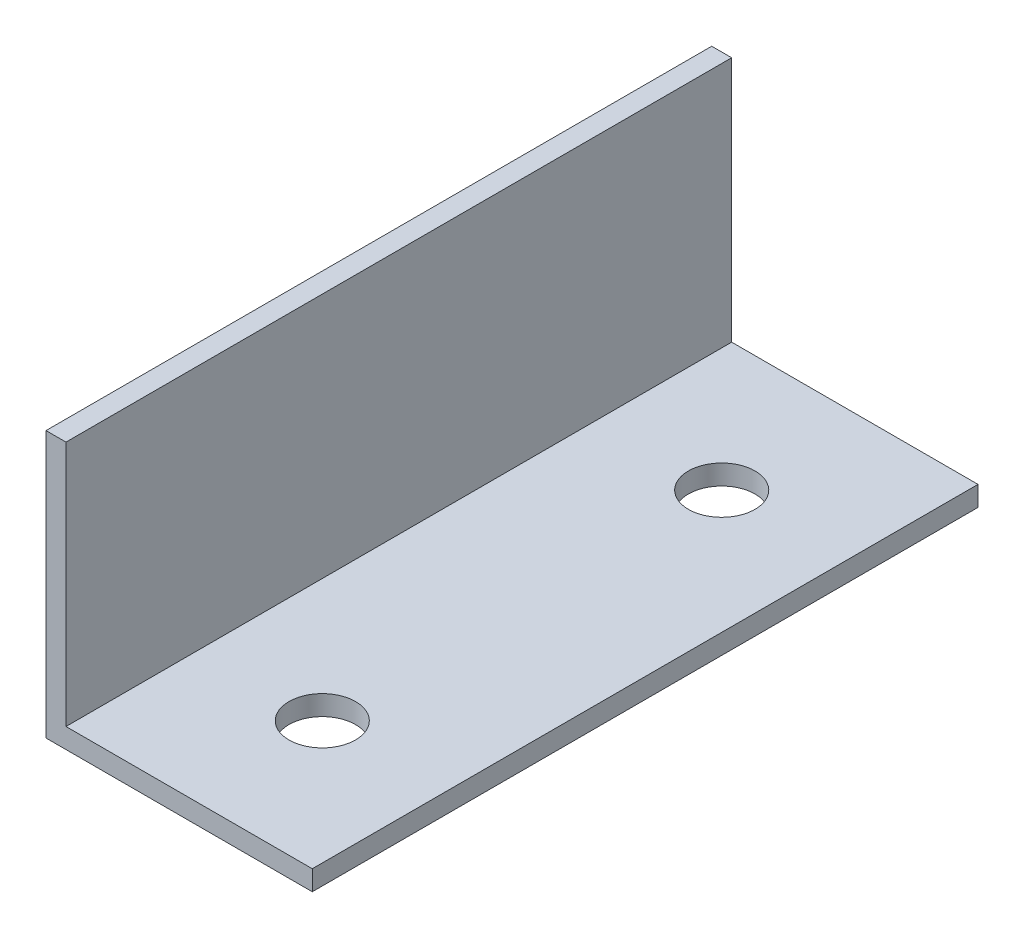
SolidWorks part; units mm, degrees
ref_plane "Спереди" through (0, 0, 0) normal (0, 0, 1) x (1, 0, 0)
ref_plane "Сверху" through (0, 0, 0) normal (0, 1, 0) x (1, 0, 0)
ref_plane "Справа" through (0, 0, 0) normal (1, 0, 0) x (0, 0, -1)
sketch "Эскиз1" plane through (0, 0, 0) normal (0, 0, 1) x (1, 0, 0)
  line L0 (0, 0) -> (0, 40)
  line L1 (0, 40) -> (3, 40)
  line L2 (3, 40) -> (3, 3)
  line L3 (3, 3) -> (40, 3)
  line L4 (40, 3) -> (40, 0)
  line L5 (40, 0) -> (0, 0)
  dimension "D1" = 40
  dimension "D2" = 40
  dimension "D3" = 3
  dimension "D4" = 3
extrude "Бобышка-Вытянуть1" add sketch "Эскиз1" along normal blind 100
sketch "Эскиз2" plane through (0, 3, 0) normal (0, 1, 0) x (1, 0, 0)
  line L0 (21.5, 0) -> (21.5, -100) construction
  line L1 (40, 0) -> (3, 0) construction
  line L2 (40, -100) -> (3, -100) construction
  circle A0 centre (21.5, -20) radius 5
  circle A1 centre (21.5, -80) radius 5
  dimension "D1" = 10
  dimension "D2" = 10
  dimension "D3" = 20
  dimension "D4" = 20
extrude "Вырез-Вытянуть1" cut sketch "Эскиз2" against normal up to next
